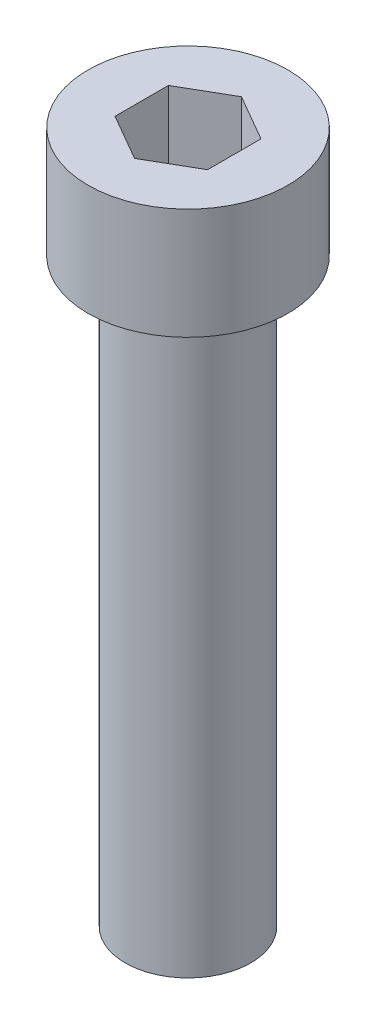
SolidWorks part; units mm, degrees
ref_plane "Front Plane" through (0, 0, 0) normal (0, 0, 1) x (1, 0, 0)
ref_plane "Top Plane" through (0, 0, 0) normal (0, 1, 0) x (1, 0, 0)
ref_plane "Right Plane" through (0, 0, 0) normal (1, 0, 0) x (0, 0, -1)
sketch "Sketch1" plane through (0, 0, 0) normal (0, 1, 0) x (1, 0, 0)
  circle A0 centre (184.7145, -125.2443) radius 2.7
  dimension "D1" = 5.4
extrude "Boss-Extrude1" add sketch "Sketch1" against normal blind 3
sketch "Sketch2" plane through (0, -3, 0) normal (0, -1, 0) x (1, 0, 0)
  circle A0 centre (184.7145, 125.2443) radius 1.6963
extrude "Boss-Extrude2" add sketch "Sketch2" along normal blind 15.7
sketch "Sketch3" plane through (0, 0, 0) normal (0, 1, 0) x (1, 0, 0)
  line L1 (184.7145, -123.8009) -> (183.4645, -124.5226)
  line L2 (183.4645, -124.5226) -> (183.4645, -125.966)
  line L3 (183.4645, -125.966) -> (184.7145, -126.6877)
  line L4 (184.7145, -126.6877) -> (185.9645, -125.966)
  line L5 (185.9645, -125.966) -> (185.9645, -124.5226)
  line L6 (185.9645, -124.5226) -> (184.7145, -123.8009)
  circle A0 centre (184.7145, -125.2443) radius 1.25 construction
  dimension "D1" = 2.5
extrude "Cut-Extrude1" cut sketch "Sketch3" against normal blind 2
